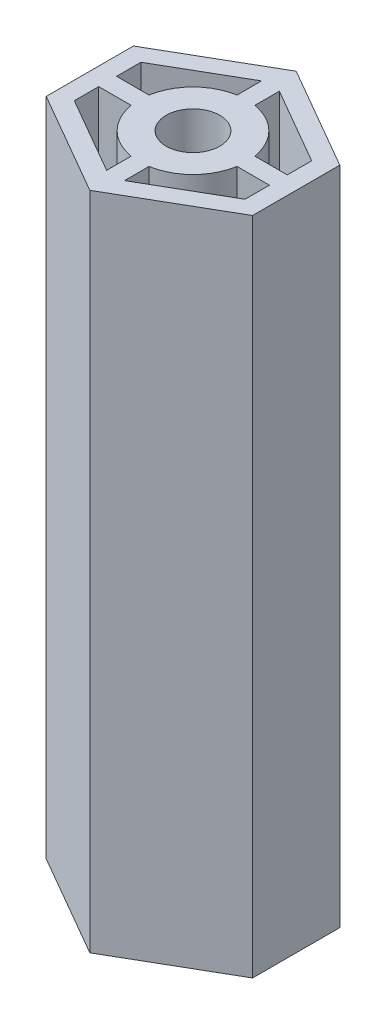
SolidWorks part; units mm, degrees
ref_plane "Front Plane" through (0, 0, 0) normal (0, 0, 1) x (1, 0, 0)
ref_plane "Top Plane" through (0, 0, 0) normal (0, 1, 0) x (1, 0, 0)
ref_plane "Right Plane" through (0, 0, 0) normal (1, 0, 0) x (0, 0, -1)
sketch "Sketch1" plane through (0, 0, 0) normal (0, 1, 0) x (1, 0, 0)
  line L0 (-12.5, 5.2831) -> (-12.5, -5.2831)
  line L1 (-12.5, 12.5) -> (12.5, 12.5) construction
  line L2 (-12.5, 12.5) -> (-12.5, -12.5) construction
  line L3 (-12.5, -12.5) -> (12.5, -12.5) construction
  line L4 (12.5, 12.5) -> (12.5, -12.5) construction
  line L5 (-12.5, -5.2831) -> (0, -12.5)
  line L6 (-12.5, 5.2831) -> (0, 12.5)
  line L7 (0, 4.0578) -> (0, -4.1758) construction
  line L8 (12.5, -5.2831) -> (0, -12.5)
  line L9 (12.5, 5.2831) -> (12.5, -5.2831)
  line L10 (12.5, 5.2831) -> (0, 12.5)
  line L11 (-1.08, 9.3823) -> (-1.08, 6.4096)
  line L12 (1.08, 9.3823) -> (1.08, 6.4096)
  line L13 (-10.34, 1.08) -> (-6.4096, 1.08)
  line L14 (-10.34, -1.08) -> (-6.4096, -1.08)
  line L15 (-1.08, -6.4096) -> (-1.08, -9.3823)
  line L16 (1.08, -6.4096) -> (1.08, -9.3823)
  line L17 (6.4096, 1.08) -> (10.34, 1.08)
  line L18 (6.4096, -1.08) -> (10.34, -1.08)
  line L19 (-10.34, 4.036) -> (-1.08, 9.3823)
  line L20 (10.34, 4.036) -> (1.08, 9.3823)
  line L21 (10.34, 4.036) -> (10.34, 1.08)
  line L22 (10.34, -4.036) -> (1.08, -9.3823)
  line L23 (-10.34, -4.036) -> (-1.08, -9.3823)
  line L24 (-10.34, 4.036) -> (-10.34, 1.08)
  line L25 (-10.34, -1.08) -> (-10.34, -4.036)
  line L26 (-10.34, 4.036) -> (-10.34, -4.036) construction
  line L27 (-10.34, -4.036) -> (0, -10.0058) construction
  line L28 (10.34, -4.036) -> (0, -10.0058) construction
  line L29 (10.34, -1.08) -> (10.34, -4.036)
  line L30 (10.34, 4.036) -> (10.34, -4.036) construction
  line L31 (-10.34, 4.036) -> (0, 10.0058) construction
  line L32 (10.34, 4.036) -> (0, 10.0058) construction
  arc A0 (-6.4096, -1.08) -> (-1.08, -6.4096) centre (0, 0) ccw
  circle A1 centre (0, 0) radius 3.25
  arc A2 (-1.08, 6.4096) -> (-6.4096, 1.08) centre (0, 0) ccw
  arc A3 (6.4096, 1.08) -> (1.08, 6.4096) centre (0, 0) ccw
  arc A4 (1.08, -6.4096) -> (6.4096, -1.08) centre (0, 0) ccw
  point P4 (-12.5, 0)
  point P5 (0, -12.5)
  point P13 (0, 12.5)
  dimension "D4" = 13
  dimension "D9" = 6.5
  dimension "D1" = 25
  dimension "D2" = 120
  dimension "D3" = 120
  dimension "D5" = 2.16
  dimension "D6" = 1.08
  dimension "D7" = 2.16
  dimension "D8" = 1.08
  dimension "D10" = 2.16
extrude "Boss-Extrude2" add sketch "Sketch1" along normal blind 80
equation "\"diameter\" = 6mm"
equation "\"D9@Sketch1\" = \"diameter\" + 0.5mm"
equation "\"D4@Sketch1\"= ( \"diameter\" + 0.5mm ) * 2"
